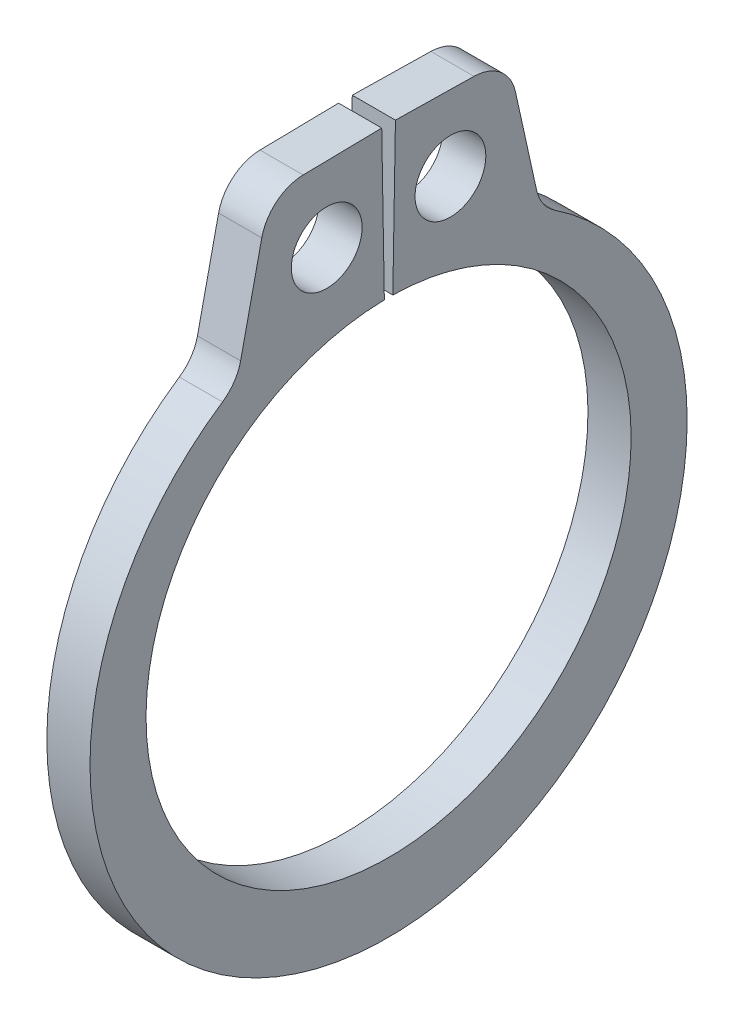
SolidWorks part; units mm, degrees
material "Cast Carbon Steel"
ref_plane "Front" through (0, 0, 0) normal (0, 0, 1) x (1, 0, 0)
ref_plane "Top" through (0, 0, 0) normal (0, 1, 0) x (1, 0, 0)
ref_plane "Right" through (0, 0, 0) normal (1, 0, 0) x (0, 0, -1)
sketch "Sketch1" plane through (0, 0, 0) normal (1, 0, 0) x (0, 0, -1)
  line L0 (0, 0) -> (0, 3.5687) construction
  line L1 (-0.0623, 3.5682) -> (-0.1008, 5.7776)
  line L2 (0.1008, 5.7776) -> (1.7579, 5.7487)
  line L3 (1.7579, 5.7487) -> (2.2341, 3.5908)
  line L4 (0.0623, 3.5682) -> (0.1008, 5.7776)
  line L5 (-0.1008, 5.7776) -> (-1.7579, 5.7487)
  line L6 (-1.7579, 5.7487) -> (-2.2341, 3.5908)
  line L7 (-2.2341, 3.5908) -> (-1.8853, 3.0301) construction
  line L8 (2.2341, 3.5908) -> (1.8853, 3.0301) construction
  line L9 (0, -3.5687) -> (0, -4.5847) construction
  line L10 (-1.7579, 5.7487) -> (-0.0623, 3.5682) construction
  line L11 (0, 3.5687) -> (0, 5.7785) construction
  line L12 (-3.5687, 0) -> (3.5687, 0) construction
  circle A0 centre (0, 0) radius 3.5687 construction
  arc A1 (-0.0623, 3.5682) -> (0.0623, 3.5682) centre (0, 0) ccw
  circle A3 centre (0, 0) radius 6.731 construction
  circle A4 centre (-0.9101, 4.6584) radius 0.5207
  circle A5 centre (0.9101, 4.6584) radius 0.5207
  arc A6 (-2.2341, 3.5908) -> (2.2341, 3.5908) centre (0, -0.1917) ccw
  point P0 (0, -4.5847)
  dimension "A" = 7.1374
  dimension "D2" = 1.6573
  dimension "L" = 13.462
  dimension "Hole" = 1.0414
  dimension "Smin" = 0.6604
  dimension "Smax" = 1.016
  dimension "H" = 2.2098
  dimension "Angle" = 1
extrude "Extrude1" add sketch "Sketch1" along normal mid plane 0.635
fillet "Fillet1" radius 0.635 4 edges at (0, 3.5908, 2.2341) (0, 3.5908, -2.2341) (0, 5.7487, 1.7579) (0, 5.7487, -1.7579)
sketch "Sketch2" plane through (0, 0, 0) normal (0, 0, 1) x (1, 0, 0)
  line L0 (-3.5433, 0) -> (9.1567, 0)
  line L1 (9.1567, 0) -> (9.1567, -3.9624)
  line L2 (-3.5433, 0) -> (-3.5433, -3.683)
  line L3 (9.1567, -3.9624) -> (0.3683, -3.9624)
  line L4 (0.3683, -3.9624) -> (0.3683, -3.683)
  line L5 (0.3683, -3.683) -> (-0.3683, -3.683)
  line L6 (-0.3683, -3.683) -> (-0.3683, -3.9624)
  line L7 (-0.3683, -3.9624) -> (-3.5433, -3.9624) construction
  line L8 (-3.5433, -3.9624) -> (-3.5433, 0) construction
  line L9 (9.1567, 0) -> (76.391, 0) construction
  line L10 (-3.5433, -3.683) -> (-3.2639, -3.9624)
  line L11 (-3.2639, -3.9624) -> (-0.3683, -3.9624)
  point P10 (0, -3.683)
  dimension "D1" = 45
  dimension "Dg" = 7.366
  dimension "Ds" = 7.9248
  dimension "W" = 0.7366
  dimension "D2" = 12.7
  dimension "D3" = 3.175
revolve "Revolve1" [suppressed] add sketch "Sketch2" angle 360 about L9
delete or keep bodies "Body-Delete1" [suppressed] type delete bodies bodies 122
equation "\"D2@Sketch2\" = \"D1@Extrude1\"*20"
equation "\"D3@Sketch2\" = \"D2@Sketch2\"/4"
equation "\"D2@Sketch1\" = \"H@Sketch1\"*.75"
equation "\"D1@Fillet1\" = \"D1@Extrude1\""
